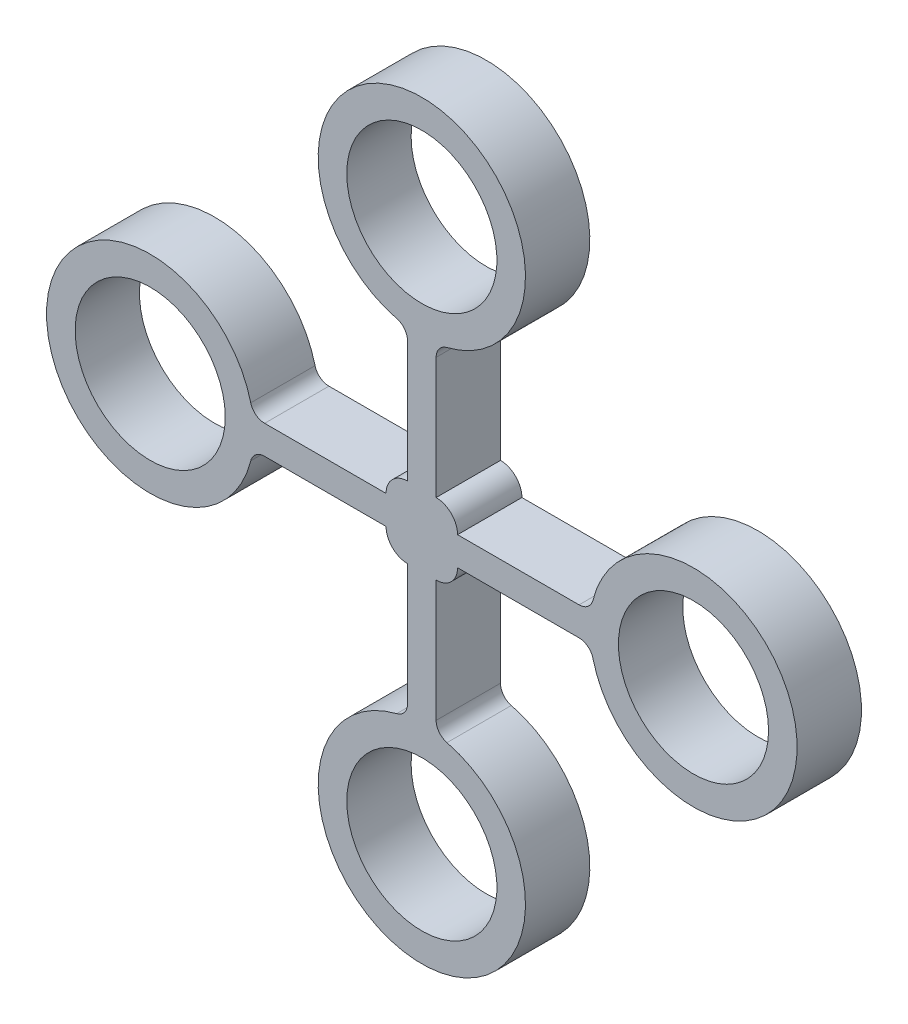
SolidWorks part; units mm, degrees
ref_plane "Front Plane" through (0, 0, 0) normal (0, 0, 1) x (1, 0, 0)
ref_plane "Top Plane" through (0, 0, 0) normal (0, 1, 0) x (1, 0, 0)
ref_plane "Right Plane" through (0, 0, 0) normal (1, 0, 0) x (0, 0, -1)
sketch "Sketch2" plane through (0, 0, 0) normal (0, 0, 1) x (1, 0, 0)
  line L1 (-27.8617, -27.8617) -> (27.8617, 27.8617) construction
  line L2 (10, 4) -> (43.9844, 4)
  line L3 (10, -4) -> (43.9844, -4)
  line L8 (4, -10) -> (4, -43.9844)
  line L9 (-4, -10) -> (-4, -43.9844)
  line L10 (-10, -4) -> (-43.9844, -4)
  line L11 (-10, 4) -> (-43.9844, 4)
  line L16 (-4, 10) -> (-4, 43.9844)
  line L17 (4, 10) -> (4, 43.9844)
  line L18 (-13.0711, 0) -> (17.6636, 0) construction
  circle A0 centre (76, 0) radius 21
  arc A1 (47.8651, -7.0303) -> (47.8651, 7.0303) centre (76, 0) ccw
  arc A2 (47.8651, -7.0303) -> (43.9844, -4) centre (43.9844, -8) ccw
  arc A3 (47.8651, 7.0303) -> (43.9844, 4) centre (43.9844, 8) cw
  arc A4 (-4, 10) -> (-10, 4) centre (-4, 4) ccw
  arc A5 (4, 10) -> (10, 4) centre (4, 4) cw
  arc A6 (-10, -4) -> (-4, -10) centre (-4, -4) ccw
  arc A7 (4, -10) -> (10, -4) centre (4, -4) ccw
  arc A15 (-7.0303, -47.8651) -> (-4, -43.9844) centre (-8, -43.9844) ccw
  arc A16 (7.0303, -47.8651) -> (4, -43.9844) centre (8, -43.9844) cw
  arc A17 (7.0303, -47.8651) -> (-7.0303, -47.8651) centre (0, -76) cw
  circle A18 centre (0, -76) radius 21
  circle A19 centre (-76, 0) radius 21
  arc A20 (-47.8651, 7.0303) -> (-47.8651, -7.0303) centre (-76, 0) ccw
  arc A21 (-47.8651, 7.0303) -> (-43.9844, 4) centre (-43.9844, 8) ccw
  arc A22 (-47.8651, -7.0303) -> (-43.9844, -4) centre (-43.9844, -8) cw
  arc A32 (7.0303, 47.8651) -> (4, 43.9844) centre (8, 43.9844) ccw
  arc A33 (-7.0303, 47.8651) -> (-4, 43.9844) centre (-8, 43.9844) cw
  arc A34 (-7.0303, 47.8651) -> (7.0303, 47.8651) centre (0, 76) cw
  circle A35 centre (0, 76) radius 21
  point P16 (0, 0)
  point P18 (0, 0)
  dimension "D1" = 8
  dimension "D2" = 42
  dimension "D5" = 4
  dimension "D6" = 4
  dimension "D10" = 10
  dimension "D8" = 6
  dimension "D3" = 76
  dimension "D4" = 8
  dimension "D7" = 10
  dimension "D9" = 4
  dimension "D11" = 45
extrude "Boss-Extrude1" add sketch "Sketch2" along normal blind 18
